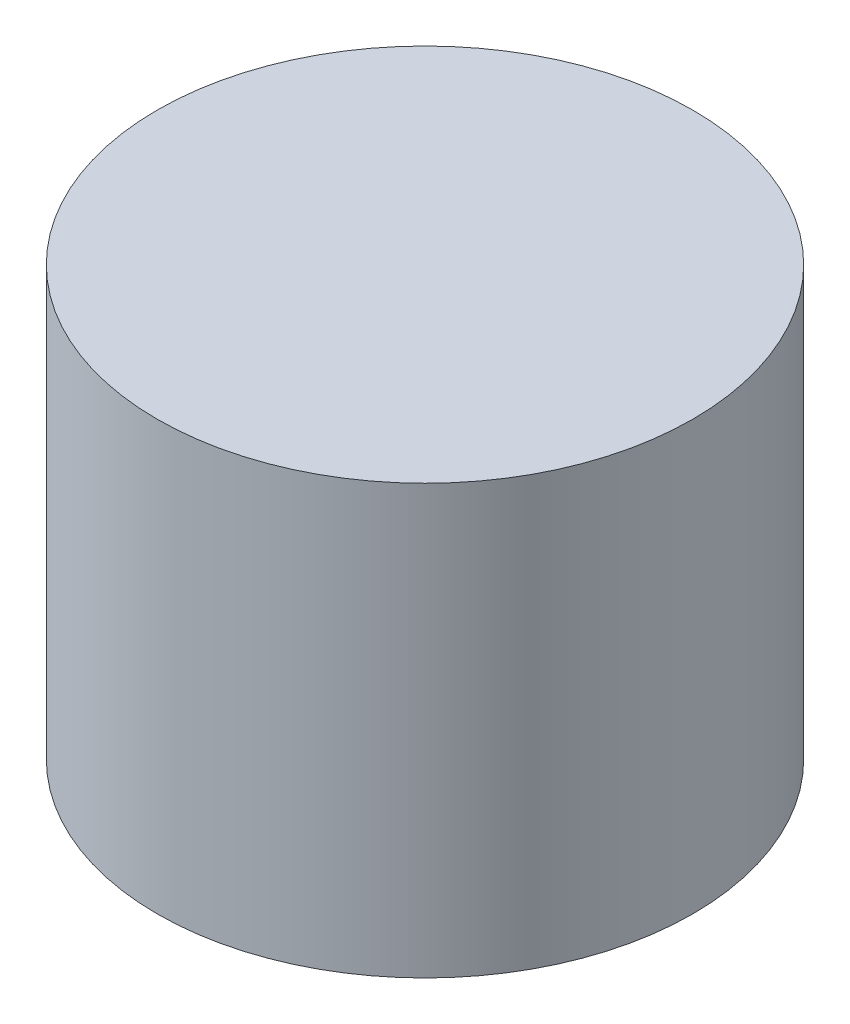
SolidWorks part; units mm, degrees
ref_plane "Front Plane" through (0, 0, 0) normal (0, 0, 1) x (1, 0, 0)
ref_plane "Top Plane" through (0, 0, 0) normal (0, 1, 0) x (1, 0, 0)
ref_plane "Right Plane" through (0, 0, 0) normal (1, 0, 0) x (0, 0, -1)
sketch "Sketch1" plane through (0, 0, 0) normal (0, 1, 0) x (1, 0, 0)
  circle A0 centre (0, 0) radius 12.5
  dimension "D1" = 25
extrude "Boss-Extrude1" add sketch "Sketch1" along normal blind 20
sketch "Sketch2" plane through (0, 0, 0) normal (0, -1, 0) x (1, 0, 0)
  circle A0 centre (0, 0) radius 2
  dimension "D1" = 4
extrude "Cut-Extrude1" cut sketch "Sketch2" against normal blind 5
